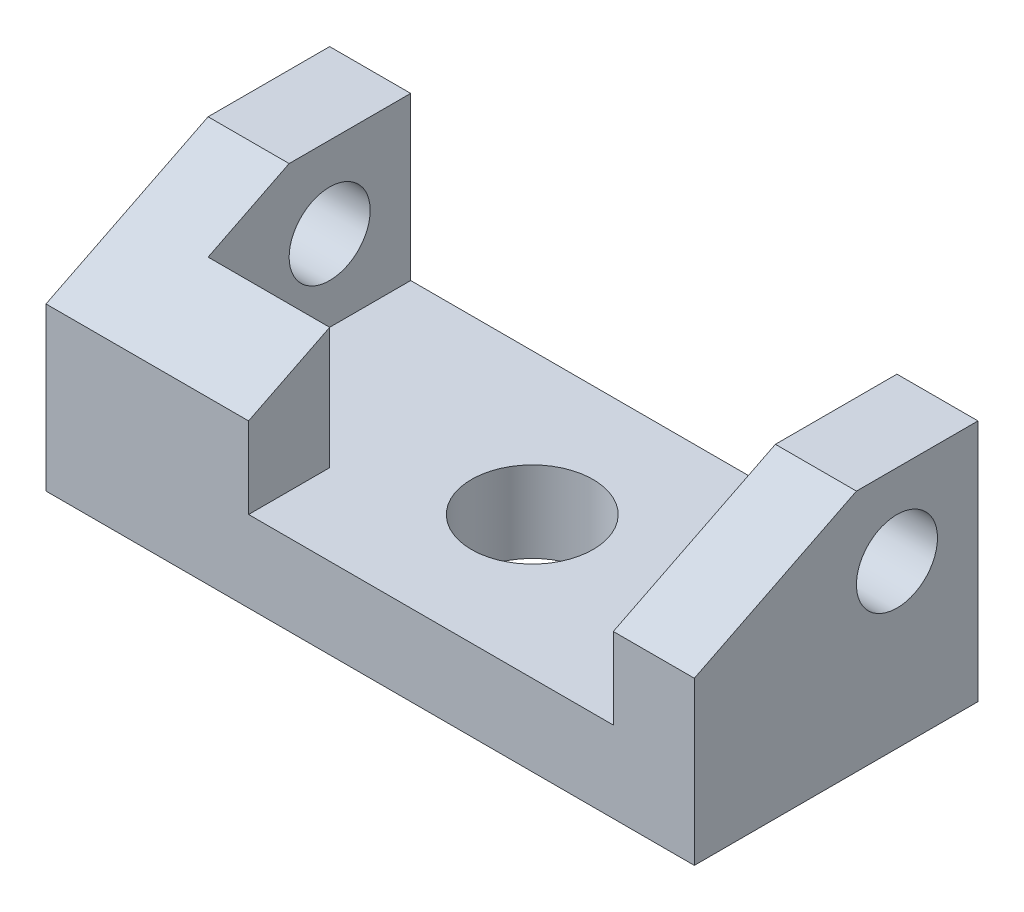
SolidWorks part; units mm, degrees
ref_plane "Front Plane" through (0, 0, 0) normal (0, 0, 1) x (1, 0, 0)
ref_plane "Top Plane" through (0, 0, 0) normal (0, 1, 0) x (1, 0, 0)
ref_plane "Right Plane" through (0, 0, 0) normal (1, 0, 0) x (0, 0, -1)
sketch "Sketch1" plane through (0, 0, 0) normal (0, 1, 0) x (1, 0, 0)
  line L1 (0, 0) -> (80, 0)
  line L2 (0, 0) -> (0, 35)
  line L3 (0, 35) -> (80, 35)
  line L4 (80, 0) -> (80, 35)
  dimension "D1" = 80
  dimension "D2" = 35
extrude "Boss-Extrude1" add sketch "Sketch1" along normal blind 30
sketch "Sketch2" plane through (0, 30, 0) normal (0, 1, 0) x (1, 0, 0)
  line L0 (0, 35) -> (10, 35) construction
  line L1 (80, 35) -> (0, 35) construction
  line L2 (80, 35) -> (70, 35) construction
  line L3 (10, 35) -> (10, 10.0024)
  line L4 (10, 10.0024) -> (25, 10.0024)
  line L5 (25, 10.0024) -> (25, 0)
  line L6 (0, 0) -> (80, 0) construction
  line L7 (25, 0) -> (70, 0)
  line L8 (70, 0) -> (70, 35)
  line L9 (70, 35) -> (10, 35)
  dimension "D1" = 10
  dimension "D2" = 10
  dimension "D3" = 15
extrude "Cut-Extrude1" cut sketch "Sketch2" against normal blind 20
sketch "Sketch3" plane through (0, 0, 0) normal (-1, 0, 0) x (0, 0, 1)
  line L0 (0, 30) -> (0, 20)
  line L1 (0, 30) -> (0, 0) construction
  line L2 (0, 20) -> (-20, 30)
  line L3 (-35, 30) -> (0, 30) construction
  line L4 (-20, 30) -> (0, 30)
  dimension "D1" = 20
  dimension "D2" = 10
extrude "Cut-Extrude2" cut sketch "Sketch3" against normal through all
sketch "Sketch4" plane through (80, 0, 0) normal (1, 0, 0) x (0, 0, -1)
  line L0 (35, 30) -> (35, 20) construction
  line L1 (35, 30) -> (35, 0) construction
  line L2 (35, 20) -> (25, 20) construction
  circle A0 centre (25, 20) radius 5
  point P7 (30.5638, 22.0141)
  dimension "D1" = 10
  dimension "D2" = 10
extrude "Cut-Extrude4" cut sketch "Sketch4" against normal through all contours A0
sketch "Sketch5" plane through (0, 10, 0) normal (0, 1, 0) x (1, 0, 0)
  line L0 (70, 0) -> (50, 0) construction
  line L1 (25, 0) -> (70, 0) construction
  line L2 (50, 0) -> (50, 17.5) construction
  line L3 (50, 17.5) -> (42.5, 17.5) construction
  circle A0 centre (42.5, 17.5) radius 7.5
  dimension "D1" = 7.5
  dimension "D2" = 17.5
  dimension "D3" = 20
extrude "Cut-Extrude5" cut sketch "Sketch5" against normal through all
